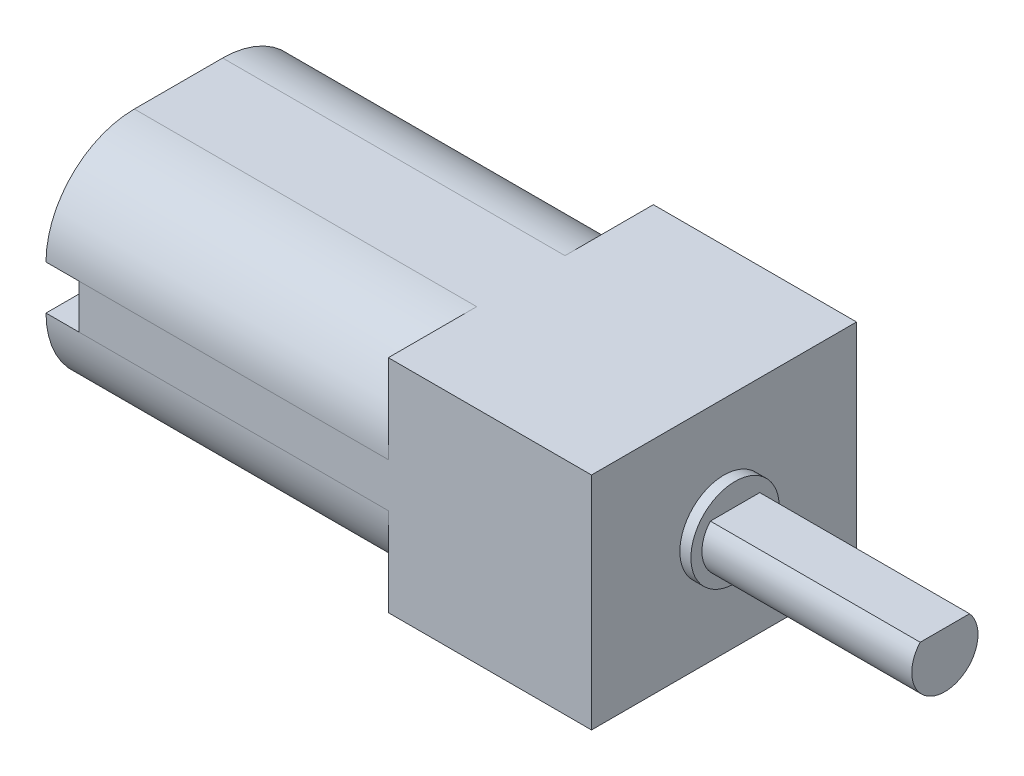
SolidWorks part; units mm, degrees
ref_plane "Front Plane" through (0, 0, 0) normal (0, 0, 1) x (1, 0, 0)
ref_plane "Top Plane" through (0, 0, 0) normal (0, 1, 0) x (1, 0, 0)
ref_plane "Right Plane" through (0, 0, 0) normal (1, 0, 0) x (0, 0, -1)
sketch "Sketch1" plane through (0, 0, 0) normal (0, 1, 0) x (1, 0, 0)
  line L1 (-4.6, -6) -> (4.6, -6)
  line L2 (-4.6, -6) -> (-4.6, 6)
  line L3 (-4.6, 6) -> (4.6, 6)
  line L4 (4.6, -6) -> (4.6, 6)
  line L5 (-4.6, -6) -> (4.6, 6) construction
  line L6 (-4.6, 6) -> (4.6, -6) construction
  point P0 (0, 0)
  dimension "D1" = 9.2
  dimension "D2" = 12
extrude "Boss-Extrude1" add sketch "Sketch1" along normal mid plane 10
sketch "Sketch3" plane through (4.6, 0, 0) normal (1, 0, 0) x (0, 0, -1)
  circle A0 centre (0, 0) radius 2
extrude "Boss-Extrude2" add sketch "Sketch3" along normal blind 0.5
sketch "Sketch4" plane through (5.1, 0, 0) normal (1, 0, 0) x (0, 0, -1)
  circle A0 centre (0, 0) radius 1.5
extrude "Boss-Extrude3" add sketch "Sketch4" along normal blind 9.5
sketch "Sketch5" plane through (14.6, 0, 0) normal (1, 0, 0) x (0, 0, -1)
  line L0 (-1.118, 1) -> (1.118, 1)
  arc A0 (1.118, 1) -> (-1.118, 1) centre (0, 0) ccw
extrude "Cut-Extrude1" cut sketch "Sketch5" against normal blind 9.5
sketch "Sketch7" plane through (-4.6, 0, 0) normal (-1, 0, 0) x (0, 0, 1)
  line L1 (-2, -5) -> (2, -5)
  line L2 (-6, -1) -> (-6, 1)
  line L3 (-2, 5) -> (2, 5)
  line L4 (6, -1) -> (6, 1)
  line L5 (-6, -5) -> (6, 5) construction
  line L6 (-6, 5) -> (6, -5) construction
  arc A0 (-2, -5) -> (-6, -1) centre (-2, -1) cw
  arc A1 (2, -5) -> (6, -1) centre (2, -1) ccw
  arc A2 (2, 5) -> (6, 1) centre (2, 1) cw
  arc A3 (-6, 1) -> (-2, 5) centre (-2, 1) cw
  point P0 (0, 0)
  dimension "D1" = 4
extrude "Boss-Extrude4" add sketch "Sketch7" along normal blind 15.5
sketch "Sketch8" plane through (-20.1, 0, 0) normal (-1, 0, 0) x (0, 0, 1)
  line L3 (-6, 1) -> (-4.5, 1)
  line L4 (-4.5, 1) -> (-4.5, -1)
  line L5 (-4.5, -1) -> (-6, -1)
  line L6 (-6, 1) -> (-6, -1)
  line L7 (0, 0) -> (0, 2.0049) construction
  line L8 (6, 1) -> (4.5, 1)
  line L9 (6, 1) -> (6, -1)
  line L10 (4.5, -1) -> (6, -1)
  line L11 (4.5, 1) -> (4.5, -1)
extrude "Cut-Extrude2" cut sketch "Sketch8" against normal blind 1.5
sketch "Sketch9" plane through (-20.1, 0, 0) normal (-1, 0, 0) x (0, 0, 1)
  line L1 (-3.7, -0.5983) -> (-3.3, -0.5983)
  line L2 (-3.7, -0.5983) -> (-3.7, 0.5983)
  line L3 (-3.7, 0.5983) -> (-3.3, 0.5983)
  line L4 (-3.3, -0.5983) -> (-3.3, 0.5983)
  line L5 (-3.7, -0.5983) -> (-3.3, 0.5983) construction
  line L6 (-3.7, 0.5983) -> (-3.3, -0.5983) construction
  line L7 (0, 0) -> (0, 1.7725) construction
  line L8 (3.7, 0.5983) -> (3.3, -0.5983) construction
  line L9 (3.7, -0.5983) -> (3.3, 0.5983) construction
  line L10 (3.3, -0.5983) -> (3.3, 0.5983)
  line L11 (3.7, 0.5983) -> (3.3, 0.5983)
  line L12 (3.7, -0.5983) -> (3.7, 0.5983)
  line L13 (3.7, -0.5983) -> (3.3, -0.5983)
  point P0 (-3.5, 0)
  point P14 (3.5, 0)
extrude "Boss-Extrude5" add sketch "Sketch9" along normal blind 1.7
sketch "Sketch10" plane through (-20.1, 0, 0) normal (-1, 0, 0) x (0, 0, 1)
  circle A0 centre (0, 0) radius 2.5
extrude "Boss-Extrude6" add sketch "Sketch10" along normal blind 1.5
sketch "Sketch11" plane through (-21.6, 0, 0) normal (-1, 0, 0) x (0, 0, 1)
  circle A0 centre (0, 0) radius 1.676
extrude "Cut-Extrude3" cut sketch "Sketch11" against normal blind 0.5
